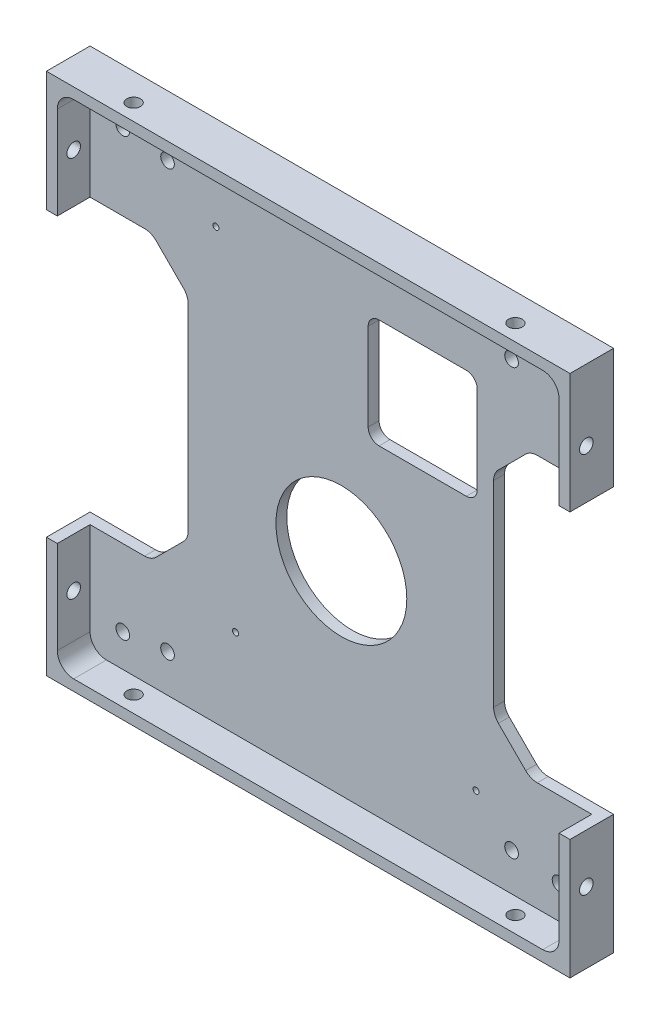
SolidWorks part; units mm, degrees
material "6061-T6 (SS)"
ref_plane "Front" through (0, 0, 0) normal (0, 0, 1) x (1, 0, 0)
ref_plane "Top" through (0, 0, 0) normal (0, 1, 0) x (1, 0, 0)
ref_plane "Right" through (0, 0, 0) normal (1, 0, 0) x (0, 0, -1)
sketch "Sketch1" plane through (0, 0, 0) normal (0, 0, 1) x (1, 0, 0)
  line L1 (-48, -48) -> (48, -48)
  line L2 (-48, -48) -> (-48, 48)
  line L3 (-48, 48) -> (48, 48)
  line L4 (48, -48) -> (48, 48)
  line L5 (-48, -48) -> (48, 48) construction
  line L6 (-48, 48) -> (48, -48) construction
  point P0 (0, 0)
  dimension "D1" = 96
  dimension "D2" = 96
extrude "Boss-Extrude1" add sketch "Sketch1" along normal blind 8
sketch "Sketch2" plane through (0, 0, 8) normal (0, 0, 1) x (1, 0, 0)
  line L1 (46, -46) -> (-46, -46)
  line L2 (46, -46) -> (46, 46)
  line L3 (46, 46) -> (-46, 46)
  line L4 (-46, -46) -> (-46, 46)
  line L5 (46, -46) -> (-46, 46) construction
  line L6 (46, 46) -> (-46, -46) construction
  point P0 (0, 0)
  dimension "D1" = 92
  dimension "D2" = 92
extrude "Component Platform" cut sketch "Sketch2" against normal blind 6
sketch "Sketch3" plane through (0, 0, 2) normal (0, 0, 1) x (1, 0, 0)
  line L1 (-33.8787, -25.1213) -> (-28.8787, -20.1213)
  line L2 (-33.8787, 25.1213) -> (-28.8787, 20.1213)
  line L3 (-28, -18) -> (-28, 18)
  line L4 (-48, -26) -> (-36, -26)
  line L7 (-48, 48) -> (-48, -48) construction
  line L8 (0, -56.7987) -> (0, 73.4321) construction
  line L9 (46, -46) -> (-57.8147, 57.8147) construction
  line L18 (46, 46) -> (-68.5705, -68.5705) construction
  line L23 (-48, 26) -> (-36, 26)
  line L26 (-48, -26) -> (-48, 26)
  line L28 (-48, -48) -> (48, -48) construction
  line L29 (48, -26) -> (48, 26)
  line L30 (48, 26) -> (36, 26)
  line L31 (33.8787, 25.1213) -> (28.8787, 20.1213)
  line L32 (28, -18) -> (28, 18)
  line L33 (33.8787, -25.1213) -> (28.8787, -20.1213)
  line L34 (48, -26) -> (36, -26)
  arc A3 (-28.8787, -20.1213) -> (-28, -18) centre (-31, -18) ccw
  arc A4 (-28.8787, 20.1213) -> (-28, 18) centre (-31, 18) cw
  arc A13 (-33.8787, -25.1213) -> (-36, -26) centre (-36, -23) cw
  arc A15 (-33.8787, 25.1213) -> (-36, 26) centre (-36, 23) ccw
  arc A17 (33.8787, 25.1213) -> (36, 26) centre (36, 23) cw
  arc A18 (28.8787, 20.1213) -> (28, 18) centre (31, 18) ccw
  arc A19 (28.8787, -20.1213) -> (28, -18) centre (31, -18) cw
  arc A20 (33.8787, -25.1213) -> (36, -26) centre (36, -23) ccw
  point P0 (-48, 0)
  point P37 (-48, 0)
  dimension "D2" = 3
  dimension "D3" = 3
  dimension "D4" = 20
  dimension "D6" = 3
  dimension "D7" = 3
  dimension "D8" = 135
  dimension "D5" = 52
  dimension "D9" = 135
  dimension "D10" = 12
  dimension "D11" = 12
  dimension "D12" = 48
extrude "Cable Slots" cut sketch "Sketch3" against normal mid plane 12
ref_plane "Center Y-Plane" through (0, 0, 0) normal (1, 0, 0) x (0, 0, -1)
ref_plane "Center X-Plane" through (0, 0, 0) normal (0, -1, 0) x (-1, 0, 0)
fillet "Inner Corner Fillets" radius 3 4 edges at (46, -46, 5) (-46, -46, 5) (46, 46, 5) (-46, 46, 5)
sketch "Sketch7" plane through (0, 0, 2) normal (0, 0, 1) x (1, 0, 0)
  line L0 (-48, -48) -> (48, -48) construction
  line L4 (48, -48) -> (48, -26) construction
  line L5 (48, 26) -> (48, 48) construction
  line L7 (48, 48) -> (-48, 48) construction
  line L8 (-43, -46) -> (43, -46) construction
  point P1 (-19.32, -29.75)
  point P4 (24.78, -32.85)
  point P5 (24.78, 32.85)
  point P8 (-22.92, 32.85)
  point P12 (24.7, -56.85)
  point P13 (24.7, 48)
  point P14 (-19.4, -48)
  point P15 (48, -32.85)
  point P16 (-48, -32.85)
  point P18 (-19.4, 48)
  point P19 (48, -32.85)
  point P20 (-48, -32.85)
  point P24 (48, 43.7)
  point P25 (-48.7506, 43.7)
  point P27 (48, 32.85)
  point P28 (-23, -48)
  point P29 (-23, 48)
  point P31 (-48.7506, 32.85)
  dimension "D1" = 16.25
  dimension "D2" = 47.7
  dimension "D3" = 15.15
  dimension "D4" = 23.22
  dimension "D5" = 23.22
  dimension "D6" = 44.1
  dimension "D7" = 15.15
  dimension "D8" = 15.15
sketch "Sketch9" plane through (0, 0, 2) normal (0, 0, 1) x (1, 0, 0)
  line L0 (25, 31) -> (25, 15)
  line L1 (23, 33) -> (7, 33)
  line L2 (23, 13) -> (7, 13)
  line L5 (5, 15) -> (5, 31)
  line L6 (48, 26) -> (48, 48) construction
  line L8 (48, 48) -> (-48, 48) construction
  arc A1 (25, 15) -> (23, 13) centre (23, 15) cw
  arc A2 (25, 31) -> (23, 33) centre (23, 31) ccw
  arc A3 (7, 33) -> (5, 31) centre (7, 31) ccw
  arc A4 (5, 15) -> (7, 13) centre (7, 15) ccw
  point P15 (25, 33)
  dimension "D1" = 2
  dimension "D6" = 2
  dimension "D7" = 16
  dimension "D2" = 20
  dimension "D3" = 16
  dimension "D4" = 15
  dimension "D5" = 23
sketch "Sketch11" plane through (48, 0, 0) normal (1, 0, 0) x (0, 0, -1)
  line L0 (-5, -48) -> (-5, 48) construction
  line L1 (-8, -48) -> (0, -48) construction
  line L2 (-8, 48) -> (0, 48) construction
  line L3 (-8, -48) -> (-8, -26) construction
  dimension "D1" = 3
sketch "Sketch12" plane through (0, 48, 0) normal (0, 1, 0) x (1, 0, 0)
  line L0 (-48, -5) -> (48, -5) construction
  line L1 (-48, -8) -> (-48, 0) construction
  line L2 (48, -8) -> (48, 0) construction
  line L3 (48, -8) -> (-48, -8) construction
  dimension "D1" = 3
hole_wizard "M3x0.5 Tapped Hole1" positions "Sketch13" profile "Sketch14" tap size "M3x0.5" standard "ANSI Metric"
sketch "Sketch13" plane through (48, 0, 0) normal (1, 0, 0) x (0, 0, -1)
  line L0 (-5, -48) -> (-5, 48) construction
  point P0 (-5, -35)
  point P4 (-5, 35)
  dimension "D1" = 70
  dimension "D2" = 35
sketch "Sketch14" plane through (48, -35, 5) normal (0, 1, 0) x (0, 0, -1)
  line L0 (0, 0) -> (0, 10.7511)
  line L1 (0, 10.7511) -> (1.25, 10)
  line L2 (1.25, 10) -> (1.25, 0)
  line L5 (1.25, 0) -> (0, 0)
  line L10 (0, 10.7511) -> (-1.25, 10) construction
  line L11 (0, -6.35) -> (0, 107.95) construction
  dimension "Tap Drill Dia." = 2.5
  dimension "Tap Drill Depth" = 10
  dimension "Drill Angle" = 118
hole_wizard "M3x0.5 Tapped Hole2" positions "Sketch15" profile "Sketch16" tap size "M3x0.5" standard "ANSI Metric"
sketch "Sketch15" plane through (0, 48, 0) normal (0, 1, 0) x (1, 0, 0)
  line L0 (-48, -5) -> (48, -5) construction
  point P0 (35, -5)
  point P4 (-35, -5)
  dimension "D1" = 70
  dimension "D2" = 35
sketch "Sketch16" plane through (35, 48, 5) normal (1, 0, 0) x (0, 0, 1)
  line L0 (0, 0) -> (0, 10.7511)
  line L1 (0, 10.7511) -> (1.25, 10)
  line L2 (1.25, 10) -> (1.25, 0)
  line L5 (1.25, 0) -> (0, 0)
  line L10 (0, 10.7511) -> (-1.25, 10) construction
  line L11 (0, -6.35) -> (0, 107.95) construction
  dimension "Tap Drill Dia." = 2.5
  dimension "Tap Drill Depth" = 10
  dimension "Drill Angle" = 118
mirror "Mirror1" about plane through (0, 0, 0) normal (1, 0, 0) of "M3x0.5 Tapped Hole1"
mirror "Mirror2" about plane through (0, 0, 0) normal (0, -1, 0) of "M3x0.5 Tapped Hole2"
sketch "Sketch22" plane through (0, 0, 2) normal (0, 0, 1) x (1, 0, 0)
  line L2 (46, -43) -> (46, -26) construction
  line L3 (-43, -46) -> (43, -46) construction
  line L4 (-46, -26) -> (-46, -43) construction
  line L6 (46, 26) -> (46, 43) construction
  line L7 (43, 46) -> (-43, 46) construction
  line L8 (-46, 43) -> (-46, 26) construction
  point P0 (-31.791, -39.06)
  point P1 (-31.791, 38.94)
  point P2 (31.29, 38.94)
  point P3 (31.29, -39.06)
  dimension "D1" = 14.71
  dimension "D2" = 6.94
  dimension "D3" = 6.94
  dimension "D4" = 14.209
  dimension "D5" = 14.71
  dimension "D6" = 7.06
  dimension "D7" = 7.06
  dimension "D8" = 14.209
hole_wizard "M1.4x0.3 Tapped Hole1" positions "Sketch27" profile "Sketch28" tap size "M1.4x0.3" standard "ANSI Metric"
sketch "Sketch27" plane through (0, 0, 2) normal (0, 0, 1) x (1, 0, 0)
  point P0 (-19.32, -29.75)
  point P3 (24.78, -32.85)
  point P9 (-22.92, 32.85)
sketch "Sketch28" plane through (-19.32, -29.75, 2) normal (1, 0, 0) x (0, -1, 0)
  line L0 (0, 0) -> (0, 4.0305)
  line L1 (0, 4.0305) -> (0.55, 3.7)
  line L2 (0.55, 3.7) -> (0.55, 0)
  line L5 (0.55, 0) -> (0, 0)
  line L10 (0, 4.0305) -> (-0.55, 3.7) construction
  line L11 (0, -6.35) -> (0, 107.95) construction
  dimension "Tap Drill Dia." = 1.1
  dimension "Tap Drill Depth" = 3.7
  dimension "Drill Angle" = 118
sketch "Sketch29" plane through (0, 0, 0) normal (0, 0, -1) x (-1, 0, 0)
  line L0 (28, 18) -> (28, -18) construction
  line L2 (48, -48) -> (-48, -48) construction
  circle A0 centre (-0.0819, -8.7479) radius 12
  dimension "D1" = 24
  dimension "D2" = 28.0819
  dimension "D3" = 39.2521
extrude "HDD Extrusion Cutout" cut sketch "Sketch29" against normal blind 10
extrude "HDD Extrusion Cutout 2" cut sketch "Sketch9" against normal blind 10
hole_wizard "M3x0.5 Tapped Hole3" positions "Sketch30" profile "Sketch31" tap size "M3x0.5" standard "ANSI Metric"
sketch "Sketch30" plane through (0, 0, 2) normal (0, 0, 1) x (1, 0, 0)
  point P0 (-31.791, -39.06)
  point P3 (31.29, -39.06)
  point P6 (31.29, 38.94)
  point P9 (-31.791, 38.94)
sketch "Sketch31" plane through (-31.791, -39.06, 2) normal (1, 0, 0) x (0, -1, 0)
  line L0 (0, 0) -> (0, 10.7511)
  line L1 (0, 10.7511) -> (1.25, 10)
  line L2 (1.25, 10) -> (1.25, 0)
  line L5 (1.25, 0) -> (0, 0)
  line L10 (0, 10.7511) -> (-1.25, 10) construction
  line L11 (0, -6.35) -> (0, 107.95) construction
  dimension "Tap Drill Dia." = 2.5
  dimension "Tap Drill Depth" = 10
  dimension "Drill Angle" = 118
sketch "Sketch32" plane through (0, 0, 2) normal (0, 0, 1) x (1, 0, 0)
  line L0 (0, -46) -> (0, 46) construction
  line L1 (-43, -46) -> (43, -46) construction
  line L2 (43, 46) -> (-43, 46) construction
  line L3 (48.3015, 0) -> (-47.2615, 0) construction
  line L5 (-48, -48) -> (48, -48) construction
  line L7 (40, 40) -> (-40, 40)
  line L8 (40, 40) -> (40, -40)
  line L9 (40, -40) -> (-40, -40)
  line L10 (-40, 40) -> (-40, -40)
  line L11 (40, 40) -> (-40, -40) construction
  line L12 (40, -40) -> (-40, 40) construction
  point P8 (0, 0)
  dimension "D1" = 48
  dimension "D2" = 80
  dimension "D3" = 80
hole_wizard "M3x0.5 Tapped Hole4" positions "Sketch33" profile "Sketch34" tap size "M3x0.5" standard "ANSI Metric" end condition through all
sketch "Sketch33" plane through (0, 0, 2) normal (0, 0, 1) x (1, 0, 0)
  point P0 (40, -40)
  point P3 (-40, -40)
  point P6 (-40, 40)
  point P9 (40, 40)
sketch "Sketch34" plane through (40, -40, 2) normal (1, 0, 0) x (0, -1, 0)
  line L0 (0, 0) -> (0, 2)
  line L1 (0, 2) -> (1.25, 2)
  line L2 (1.25, 2) -> (1.25, 0)
  line L5 (1.25, 0) -> (0, 0)
  line L11 (0, -6.35) -> (0, 107.95) construction
  dimension "Thru Tap Drill Dia." = 2.5
  dimension "Thru Tap Drill Depth" = 2
cosmetic thread "Hole Thread1" parameters "D2"=3
cosmetic thread "Hole Thread2" parameters "D2"=3
cosmetic thread "Hole Thread3" parameters "D2"=3
cosmetic thread "Hole Thread4" parameters "D2"=3
